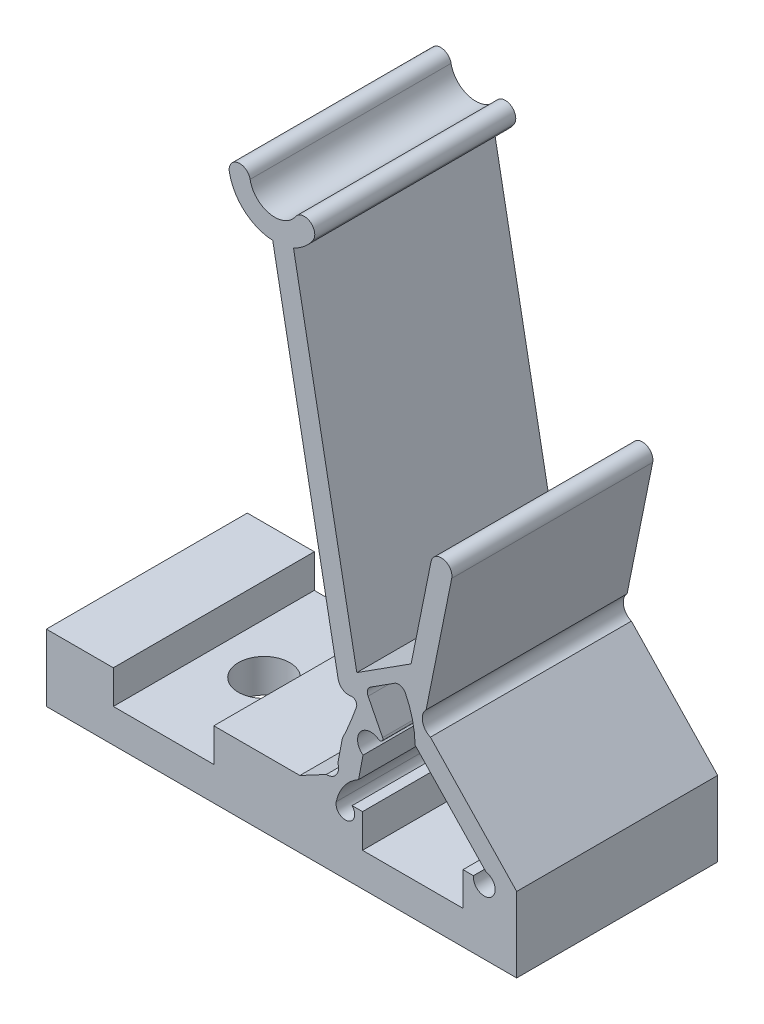
SolidWorks part; units mm, degrees
ref_plane "Front Plane" through (0, 0, 0) normal (0, 0, 1) x (1, 0, 0)
ref_plane "Top Plane" through (0, 0, 0) normal (0, 1, 0) x (1, 0, 0)
ref_plane "Right Plane" through (0, 0, 0) normal (1, 0, 0) x (0, 0, -1)
sketch "Sketch-SkeletonConfigUp" plane through (0, 0, 0) normal (0, 0, 1) x (1, 0, 0)
  line L0 (0, 0) -> (0, -50000) construction
  line L1 (0, 0) -> (7.455, 0.2734) construction
  line L2 (9.9233, 0.3639) -> (10.6101, 4.558) construction
  line L3 (10.6101, 4.558) -> (7.9471, 2.8569) construction
  line L4 (7.9471, 2.8569) -> (7.455, 0.2734) construction
  line L5 (10.6101, 4.558) -> (12.0093, 11.478) construction
  line L6 (7.9471, 2.8569) -> (4.1146, 23.199) construction
  line L7 (7.455, 0.2734) -> (9.9233, 0.3639) construction
  line L8 (-989.4051, -36.2798) -> (9.9233, 0.3639) construction
  point P12 (0, 0)
  point P16 (0, 0)
  point P17 (0, 0)
  dimension "D2" = 7.46
  dimension "D3" = 2.47
  dimension "D4" = 4.25
  dimension "D5" = 78.6
  dimension "D6" = 3.16
  dimension "D7" = 7.06
  dimension "D8" = 20.7
  dimension "D9" = 2.63
  dimension "D10" = 46
  dimension "D11" = 111.9
  dimension "D12" = 92.1
sketch "Sketch-SkeletonConfigDown" plane through (0, 0, 0) normal (0, 0, 1) x (1, 0, 0)
  line L0 (0, 0) -> (0, -50000) construction
  line L1 (0, 0) -> (7.455, 0.2734) construction
  line L2 (9.9233, 0.3639) -> (10.6101, 4.558) construction
  line L3 (10.6101, 4.558) -> (9.7761, 1.5101) construction
  line L4 (9.7761, 1.5101) -> (7.455, 0.2734) construction
  line L5 (10.6101, 4.558) -> (7.0062, 10.6288) construction
  line L6 (9.7761, 1.5101) -> (-6.7111, 14.0265) construction
  line L7 (7.455, 0.2734) -> (9.9233, 0.3639) construction
  line L8 (-993.745, -36.439) -> (9.9233, 0.3639) construction
  point P2 (10.901, 5.6207)
  dimension "D2" = 7.46
  dimension "D3" = 2.47
  dimension "D4" = 4.25
  dimension "D5" = 78.6
  dimension "D6" = 3.16
  dimension "D7" = 7.06
  dimension "D8" = 20.7
  dimension "D9" = 2.63
  dimension "D10" = 46
  dimension "D11" = 111.9
  dimension "D1" = 92.1
sketch "Sketch-ConfigDown" plane through (0, 0, 0) normal (0, 0, 1) x (1, 0, 0)
  line L3 (7.2122, -0.2359) -> (5.3047, -0.3058) construction
  line L4 (9.7761, 1.5101) -> (-6.7111, 14.0265) construction
  line L6 (-200859.4238, -7365.1807) -> (9.9233, 0.3639) construction
  line L7 (7.2122, -0.2359) -> (15.5786, 0.0709) construction
  line L9 (7.455, 0.2734) -> (9.9233, 0.3639) construction
  line L10 (10.9008, 0.9001) -> (10.9374, -0.0993) construction
  line L15 (9.3493, 0.7161) -> (8.352, 0.1848)
  line L18 (8.512, 1.4031) -> (8.9823, 0.5206) construction
  line L19 (6.5762, 10.3736) -> (9.0074, 6.2784)
  line L20 (-5.3148, 12.3387) -> (8.4132, 1.917)
  line L21 (8.2015, 3.3332) -> (-4.7101, 13.1352)
  line L22 (9.7761, 1.5101) -> (7.455, 0.2734) construction
  line L23 (2.9291, 6.0802) -> (3.5338, 6.8767) construction
  line L26 (10.6101, 4.558) -> (14.4503, 0.5299) construction
  line L27 (10.2553, 5.1557) -> (9.3507, 1.85) construction
  line L28 (11.0112, 4.862) -> (15.5786, 0.0709) construction
  line L29 (14.5562, -0.3058) -> (10.7658, 3.6702) construction
  line L30 (12.9938, 1.3331) -> (13.7176, 2.0231) construction
  line L34 (5.3047, -0.3058) -> (5.3047, -3.4808) construction
  line L36 (5.3047, -3.4808) -> (15.5786, -3.4808)
  line L37 (15.5786, -3.4808) -> (15.5786, 0.0709)
  line L38 (-8.0357, 12.2817) -> (-6.0162, 14.9419) construction
  line L39 (10.6101, 4.558) -> (9.7761, 1.5101) construction
  line L40 (9.7556, 3.3297) -> (10.7202, 3.0657) construction
  line L42 (7.4361, 10.8841) -> (10.4021, 5.8879)
  line L43 (8.1032, 7.8014) -> (8.9631, 8.3119) construction
  line L44 (10.6101, 4.558) -> (7.0062, 10.6288) construction
  line L45 (7.7789, -0.3058) -> (5.3047, -0.3058) construction
  line L46 (14.5562, -0.3058) -> (15.5786, -0.3058) construction
  line L47 (13.528, -0.3058) -> (7.7789, -0.3058)
  line L48 (9.0074, 6.2784) -> (8.2015, 3.3332)
  line L49 (15.5786, 0.0709) -> (15.28, 0.3842)
  line L50 (10.7658, 3.6702) -> (9.7307, 4.7558) construction
  line L51 (15.28, 0.3842) -> (14.5562, -0.3058) construction
  line L52 (14.5815, 0.7545) -> (14.7625, 0.927) construction
  line L53 (13.5212, 0.7799) -> (14.2449, 1.4699) construction
  line L54 (11.0112, 4.862) -> (10.4545, 5.4459) construction
  line L55 (10.7911, 4.7305) -> (10.972, 4.903) construction
  line L56 (9.7307, 4.7558) -> (10.4545, 5.4459) construction
  line L57 (10.7658, 3.6702) -> (11.4896, 4.3602) construction
  line L58 (10.7911, 4.7305) -> (10.4292, 4.3855) construction
  line L59 (11.4896, 4.3602) -> (14.2449, 1.4699)
  line L60 (13.5212, 0.7799) -> (10.7658, 3.6702)
  line L61 (10.4545, 5.4459) -> (10.4021, 5.8879)
  line L62 (7.3374, 0.494) -> (7.2199, 0.7146) construction
  line L63 (7.0282, -0.5206) -> (6.3041, -0.9064) construction
  line L64 (7.8818, 1.0673) -> (8.352, 0.1848) construction
  line L65 (6.558, 0.362) -> (7.0282, -0.5206) construction
  line L66 (6.558, 0.362) -> (5.3047, -0.3058)
  line L67 (6.558, 0.362) -> (7.8818, 1.0673) construction
  line L68 (7.3374, 0.494) -> (7.5725, 0.0527) construction
  line L69 (10.2029, 2.304) -> (10.8079, 2.6264) construction
  line L70 (10.6731, 1.4215) -> (11.1125, 1.6556) construction
  line L71 (9.6585, 1.7307) -> (9.541, 1.9513) construction
  line L72 (8.8791, 1.5987) -> (9.3493, 0.7161) construction
  line L73 (10.2029, 2.304) -> (10.6731, 1.4215) construction
  line L74 (9.6585, 1.7307) -> (9.8936, 1.2894) construction
  line L75 (7.8818, 1.0673) -> (8.8791, 1.5987)
  line L76 (8.4132, 1.917) -> (9.4143, 2.4504)
  line L77 (9.6228, 4.1445) -> (11.1323, 2.561)
  line L78 (11.1323, 2.561) -> (11.3028, 2.3822)
  line L79 (-6.7111, 14.0265) -> (-5.0362, 14.2558) construction
  line L80 (-6.7111, 14.0265) -> (-6.7111, -3.4808) construction
  line L81 (5.3047, -3.4808) -> (-6.7111, -3.4808)
  line L82 (-6.7111, -3.4808) -> (-6.7111, -0.3058)
  line L83 (-6.7111, -0.3058) -> (5.3047, -0.3058)
  line L84 (8.8791, 1.5987) -> (10.2029, 2.304) construction
  arc A2 (-7.4311, 13.0782) -> (-5.5316, 14.188) centre (-6.7111, 14.0265) ccw
  arc A3 (-4.7101, 13.1352) -> (-4.5408, 14.3236) centre (-6.7111, 14.0265) ccw
  arc A4 (-8.0357, 12.2817) -> (-7.4311, 13.0782) centre (-7.7334, 12.68) cw
  arc A5 (-4.5408, 14.3236) -> (-5.5316, 14.188) centre (-5.0362, 14.2558) ccw
  arc A6 (-8.0357, 12.2817) -> (-5.3148, 12.3387) centre (-6.7111, 14.0265) ccw
  arc A7 (6.5762, 10.3736) -> (7.4361, 10.8841) centre (7.0062, 10.6288) cw
  arc A8 (15.28, 0.3842) -> (14.2449, 1.4699) centre (15.4863, 1.6171) cw
  arc A9 (14.5562, -0.3058) -> (13.5212, 0.7799) centre (13.3149, -0.453) ccw
  arc A10 (10.4545, 5.4459) -> (11.4896, 4.3602) centre (11.6958, 5.593) ccw
  arc A11 (9.7307, 4.7558) -> (10.7658, 3.6702) centre (9.5245, 3.523) cw
  arc A12 (7.8818, 1.0673) -> (6.558, 0.362) centre (6.7496, 1.5972) cw
  arc A13 (7.0282, -0.5206) -> (8.352, 0.1848) centre (8.1603, -1.0505) cw
  arc A14 (7.0282, -0.5206) -> (7.7789, -0.3058) centre (7.4971, -0.74) ccw
  arc A15 (8.8791, 1.5987) -> (10.2029, 2.304) centre (9.0707, 2.8339) ccw
  arc A16 (9.3493, 0.7161) -> (10.6731, 1.4215) centre (10.4814, 0.1863) cw
  arc A19 (10.2029, 2.304) -> (9.4143, 2.4504) centre (9.8276, 2.4796) ccw
  arc A20 (14.5562, -0.3058) -> (13.528, -0.3058) centre (14.0421, -0.3668) cw
  arc A21 (9.7307, 4.7558) -> (9.6228, 4.1445) centre (9.6795, 4.4497) ccw
  arc A22 (10.6731, 1.4215) -> (11.3028, 2.3822) centre (10.7698, 2.0448) ccw
  point P5 (0, 0)
  point P24 (8.7471, 0.9618)
  point P28 (10.9191, 0.4004)
  point P30 (8.5332, 8.0566)
  point P43 (10.2379, 3.1977)
  point P47 (14.5815, 0.7545)
  point P51 (3.2315, 6.4785)
  point P61 (13.3557, 1.6781)
  dimension "D3" = 2.3812
  dimension "D4" = 4.3812
  dimension "D1" = 1
  dimension "D8" = 1.5
  dimension "D12" = 1.5
  dimension "D5" = 1
  dimension "D6" = 7
  dimension "D2" = 3.175
  dimension "D7" = 1.5
  dimension "D9" = 1.5
  dimension "D10" = 0.25
  dimension "D11" = 1.5
  dimension "D13" = 0.5
  dimension "D14" = 0.5
  dimension "D15" = 45
sketch "Sketch-ConfigUp" plane through (0, 0, 0) normal (0, 0, 1) x (1, 0, 0)
  line L1 (7.3156, 2.2137) -> (7.1042, 1.1037)
  line L2 (8.0635, 0.796) -> (13.3219, 0.9888) construction
  line L3 (10.1988, -0.1264) -> (6.8464, -0.2493) construction
  line L4 (7.9471, 2.8569) -> (7.455, 0.2734) construction
  line L5 (11.5192, 11.5771) -> (10.5754, 6.909)
  line L6 (7.455, 0.2734) -> (9.9233, 0.3639) construction
  line L7 (10.1988, -0.1264) -> (15.5786, 0.0709) construction
  line L9 (10.6101, 4.558) -> (7.9471, 2.8569) construction
  line L10 (8.9451, 0.8283) -> (8.9817, -0.171) construction
  line L11 (7.2099, 1.6587) -> (8.1922, 1.4716) construction
  line L12 (8.7452, 3.96) -> (9.2835, 3.1173) construction
  line L15 (9.9233, 0.3639) -> (10.6101, 4.558) construction
  line L16 (9.7754, 2.5547) -> (10.7623, 2.3931) construction
  line L17 (12.4994, 11.3789) -> (11.2863, 5.379)
  line L18 (10.6101, 4.558) -> (12.0093, 11.478) construction
  line L19 (10.5058, 6.5648) -> (11.486, 6.3666) construction
  line L20 (4.0182, 21.0106) -> (7.1163, 4.5661)
  line L21 (8.0021, 5.2653) -> (5.0009, 21.1957)
  line L22 (7.9471, 2.8569) -> (4.1146, 23.199) construction
  line L23 (6.0985, 9.9681) -> (7.0813, 10.1533) construction
  line L24 (8.3015, 3.6766) -> (10.1621, 4.8651) construction
  line L26 (10.6101, 4.558) -> (14.4503, 0.5299) construction
  line L27 (-200855.0838, -7365.0216) -> (9.9233, 0.3639) construction
  line L30 (10.7658, 3.6702) -> (11.4896, 4.3602) construction
  line L34 (6.8464, -0.2493) -> (6.8464, -3.4808) construction
  line L38 (1.9619, 22.7935) -> (4.1146, 23.199) construction
  line L39 (4.1146, 23.199) -> (5.9236, 21.9636) construction
  line L40 (13.528, -0.3058) -> (7.7789, -0.3058) construction
  line L41 (13.528, -0.3058) -> (7.7789, -0.3058)
  line L42 (11.2489, 5.194) -> (10.7354, 2.6543) construction
  line L43 (10.1621, 4.8651) -> (9.715, 2.6538) construction
  line L44 (6.8464, -0.2493) -> (5.1916, -0.31) construction
  line L45 (8.0635, 0.796) -> (8.0865, 0.9166) construction
  line L46 (8.0635, 0.796) -> (7.8058, -0.5569) construction
  line L47 (7.2094, 0.3201) -> (6.9638, 0.3669) construction
  line L48 (7.2094, 0.3201) -> (7.7006, 0.2266) construction
  line L49 (6.8235, -0.3698) -> (7.8058, -0.5569) construction
  line L50 (7.4382, 2.8574) -> (7.5963, 3.6872) construction
  line L51 (8.3979, 2.5516) -> (8.5786, 3.5001) construction
  line L52 (7.3156, 2.2137) -> (8.2979, 2.0266) construction
  line L53 (7.5963, 3.6872) -> (8.5786, 3.5001) construction
  line L54 (7.7015, 2.9037) -> (8.1927, 2.8101) construction
  line L55 (7.7015, 2.9037) -> (7.4559, 2.9505) construction
  line L56 (8.1564, 2.8991) -> (7.6708, 3.0185) construction
  line L57 (7.1163, 4.5661) -> (7.4382, 2.8574) construction
  line L58 (11.2863, 5.379) -> (10.3061, 5.5772) construction
  line L59 (7.4382, 2.8574) -> (7.3156, 2.2137) construction
  line L60 (7.8068, 2.1202) -> (8.6839, 3.337) construction
  line L61 (8.2979, 2.0266) -> (8.0865, 0.9166)
  line L62 (7.1042, 1.1037) -> (8.0865, 0.9166) construction
  line L69 (10.8552, 4.5085) -> (11.1002, 4.4589) construction
  line L70 (7.7789, -0.3058) -> (5.3047, -0.3058) construction
  line L71 (7.7789, -0.3058) -> (5.3047, -0.3058) construction
  line L73 (7.1042, 1.1037) -> (6.8464, -0.2493) construction
  line L74 (10.2687, 5.3922) -> (11.2489, 5.194) construction
  line L75 (9.9714, 3.922) -> (10.9516, 3.7238) construction
  line L76 (10.8552, 4.5085) -> (10.3651, 4.6076) construction
  line L77 (8.3979, 2.5516) -> (8.2979, 2.0266) construction
  line L78 (9.5833, 3.3088) -> (8.3979, 2.5516) construction
  line L79 (8.0021, 5.2653) -> (10.5754, 6.909)
  line L80 (8.0021, 5.2653) -> (8.3015, 3.6766) construction
  line L81 (10.5058, 6.5648) -> (10.1621, 4.8651) construction
  line L82 (10.5058, 6.5648) -> (10.5754, 6.909) construction
  line L83 (11.4896, 4.3602) -> (10.7658, 3.6702) construction
  line L84 (11.1158, 4.8153) -> (10.6255, 4.7174) construction
  line L106 (6.558, 0.362) -> (5.3047, -0.3058)
  line L107 (5.3047, -0.3058) -> (-6.7111, -0.3058)
  line L108 (-6.7111, -0.3058) -> (-6.7111, -3.4808)
  line L109 (-6.7111, -3.4808) -> (15.5786, -3.4808)
  line L110 (15.5786, -3.4808) -> (15.5786, 0.0709)
  line L112 (15.5786, 0.0709) -> (11.4896, 4.3602)
  line L114 (11.1277, 4.0152) -> (10.7962, 5.4781) construction
  line L115 (9.5833, 3.3088) -> (10.5323, 3.915) construction
  line L116 (13.3219, 0.9888) -> (10.7658, 3.6702)
  line L117 (10.7658, 3.6702) -> (10.5323, 3.915) construction
  line L118 (10.6101, 4.558) -> (7.9471, 2.8569) construction
  line L119 (8.6839, 3.337) -> (9.4161, 2.8092) construction
  line L120 (8.6839, 3.337) -> (7.8068, 3.9692) construction
  line L121 (9.0288, 3.0406) -> (8.2979, 2.0266) construction
  line L123 (9.7888, 5.7212) -> (8.6571, 4.9983)
  line L124 (8.5388, 4.5661) -> (9.2253, 3.2085)
  line L126 (13.3219, 0.9888) -> (14.1275, 0.1438)
  line L127 (11.2489, 5.194) -> (11.2863, 5.379) construction
  arc A0 (11.5192, 11.5771) -> (12.4994, 11.3789) centre (12.0093, 11.478) cw
  arc A2 (2.9446, 22.9786) -> (5.0978, 22.5276) centre (4.1146, 23.199) ccw
  arc A3 (5.0009, 21.1957) -> (5.9236, 21.9636) centre (4.1146, 23.199) ccw
  arc A4 (1.9619, 22.7935) -> (2.9446, 22.9786) centre (2.4533, 22.886) cw
  arc A5 (5.9236, 21.9636) -> (5.0978, 22.5276) centre (5.5107, 22.2456) ccw
  arc A6 (1.9619, 22.7935) -> (4.0182, 21.0106) centre (4.1146, 23.199) ccw
  arc A7 (13.528, -0.3058) -> (14.5562, -0.3058) centre (14.0421, -0.3668) ccw construction
  arc A8 (13.528, -0.3058) -> (14.1275, 0.1438) centre (14.0421, -0.3668) ccw
  arc A9 (7.1042, 1.1037) -> (6.8235, -0.3698) centre (5.9815, 0.554) cw construction
  arc A10 (7.8058, -0.5569) -> (8.0865, 0.9166) centre (8.9285, -0.0073) cw construction
  arc A11 (7.3156, 2.2137) -> (7.5963, 3.6872) centre (6.4736, 3.1376) ccw construction
  arc A12 (8.2979, 2.0266) -> (8.5786, 3.5001) centre (9.4206, 2.5762) cw construction
  arc A13 (11.2489, 5.194) -> (10.9516, 3.7238) centre (12.0804, 4.2607) ccw construction
  arc A14 (10.2687, 5.3922) -> (9.9714, 3.922) centre (9.1399, 4.8553) cw construction
  arc A15 (8.0865, 0.9166) -> (7.0282, -0.5206) centre (9.1391, -0.9668) ccw
  arc A16 (7.1042, 1.1037) -> (6.558, 0.362) centre (6.5823, 0.916) cw
  arc A17 (7.0282, -0.5206) -> (7.7789, -0.3058) centre (7.4604, -0.612) ccw
  arc A18 (11.4896, 4.3602) -> (11.2863, 5.379) centre (11.7287, 4.9376) cw
  arc A19 (8.2979, 2.0266) -> (9.0288, 3.0406) centre (8.6634, 2.5336) cw
  arc A21 (7.3156, 2.2137) -> (7.9864, 3.8397) centre (-8.9784, 9.887) ccw
  arc A22 (7.9864, 3.8397) -> (7.7104, 4.1617) centre (7.7563, 3.9218) ccw
  arc A23 (10.7658, 3.6702) -> (10.3061, 5.5772) centre (6.3229, 3.6081) ccw
  arc A24 (7.7104, 4.1617) -> (7.1163, 4.5661) centre (7.615, 4.66) cw
  arc A25 (9.0288, 3.0406) -> (9.2253, 3.2085) centre (9.1066, 3.1485) ccw
  arc A27 (10.3061, 5.5772) -> (9.7888, 5.7212) centre (9.9829, 5.4174) ccw
  arc A39 (8.6571, 4.9983) -> (8.5388, 4.5661) centre (8.8369, 4.7168) ccw
  point P6 (0, 0)
  point P25 (9.0144, 3.5387)
  point P27 (7.701, 1.5651)
  point P28 (8.9634, 0.3287)
  point P36 (10.2689, 2.4739)
  point P38 (10.9959, 6.4657)
  point P51 (6.5899, 10.0607)
  point P59 (0, 0)
  point P61 (11.1277, 4.0152)
  point P65 (5.776, 23.512)
  point P71 (5.776, 23.512)
  point P82 (0, 0)
  point P86 (0, 0)
  point P107 (0, 0)
  point P120 (5.7693, 23.1882)
  point P122 (0, 0)
  point P123 (5.3047, 23.4195)
  point P126 (0, 0)
  point P127 (0, 0)
  point P128 (0, 0)
  point P163 (5.0978, 22.5276)
  dimension "D3" = 2.3812
  dimension "D4" = 4.3812
  dimension "D13" = 0.625
  dimension "D17" = 0.625
  dimension "D1" = 1
  dimension "D5" = 7
  dimension "D10" = 1.5
  dimension "D11" = 0.25
  dimension "D8" = 1.5
  dimension "D9" = 0.25
  dimension "D6" = 1.5
  dimension "D7" = 0.25
  dimension "D12" = 1.5
  dimension "D15" = 0.5
  dimension "D16" = 1.5
  dimension "D18" = 0.5
  dimension "D19" = 25
  dimension "D20" = 1.5
  dimension "D14" = 45
extrude "Boss-ConfigUp" add sketch "Sketch-ConfigUp" along normal blind 9.525
sketch "Sketch2" plane through (0.0043, -0.3058, 0) normal (0, -1, 0) x (-1, 0, 0)
  line L1 (-13.0304, 0) -> (-8.2679, 0)
  line L2 (-13.0304, 0) -> (-13.0304, -9.525)
  line L3 (-13.0304, -9.525) -> (-8.2679, -9.525)
  line L4 (-8.2679, 0) -> (-8.2679, -9.525)
  line L5 (-13.5237, 0) -> (-13.0304, 0) construction
  line L7 (-8.2679, 0) -> (-7.7746, 0) construction
  line L10 (-15.5743, -4.7625) -> (6.7155, -4.7625) construction
  line L12 (-13.0304, 0) -> (-8.2679, -9.525) construction
  line L17 (-13.0304, -9.525) -> (-8.2679, 0) construction
  line L18 (6.7155, 0) -> (-15.5743, 0) construction
  line L19 (6.7155, -9.525) -> (6.7155, 0) construction
  line L20 (3.5405, -9.525) -> (3.5405, 0)
  line L21 (3.5405, -9.525) -> (-1.222, -9.525)
  line L22 (3.5405, 0) -> (-1.222, 0)
  line L23 (-1.222, -9.525) -> (-1.222, 0)
  line L24 (3.5405, -9.525) -> (-1.222, 0) construction
  line L25 (3.5405, 0) -> (-1.222, -9.525) construction
  line L26 (6.7155, -9.525) -> (-15.5743, -9.525) construction
  line L27 (-15.5743, -9.525) -> (-15.5743, 0) construction
  point P4 (-10.6492, -4.7625)
  point P26 (1.1592, -4.7625)
  dimension "D1" = 4.7625
  dimension "D2" = 3.175
extrude "Cut-NutSlot" cut sketch "Sketch2" along normal blind 1.5875
hole_wizard "#2 Clearance Hole1" positions "Sketch4" profile "Sketch3" hole size "#2" standard "ANSI Inch" end condition up to next
sketch "Sketch4" plane through (0, -3.4808, 0) normal (0, -1, 0) x (-1, 0, 0)
  line L16 (-13.0347, 0) -> (-8.2722, -9.525) construction
  point P40 (-10.6535, -4.7625)
  point P44 (1.1549, -4.7625)
  point P47 (-10.6535, -4.7625)
  point P48 (1.1549, -4.7625)
sketch "Sketch3" plane through (10.6535, -3.4808, 4.7625) normal (1, 0, 0) x (0, 0, -1)
  line L0 (0, 0) -> (0, 1.5875)
  line L1 (0, 1.5875) -> (1.2192, 1.5875)
  line L2 (1.2192, 1.5875) -> (1.2192, 0)
  line L5 (1.2192, 0) -> (0, 0)
  line L11 (0, -6.35) -> (0, 107.95) construction
  dimension "Thru Hole Dia." = 2.4384
  dimension "Thru Hole Depth" = 1.5875
ref_plane "Plane-Midplane" through (0, 0, 4.7625) normal (0, 0, -1) x (-1, 0, 0)
equation "\"axle-diameter\"=2"
equation "\"switch-thickness\"=12"
equation "\"base-width\"=4.0"
equation "\"axle-bushing-radius\"=3"
equation "\"clearance\"= 0.25"
equation "\"arm-width\"=1.0"
equation "\"min-diameter\"=70"
equation "\"alpha\"=92.1"
equation "\"beta\"=26.0"
equation "\"gamma\"=78.6"
equation "\"delta\"=111.9"
equation "\"epsilon\"=46.0"
equation "\"eta\"=-228.1"
equation "\"l_AB\"=2.47"
equation "\"l_AC\"=2.63"
equation "\"l_BD\"=4.25"
equation "\"l_CD\"=3.16"
equation "\"l_CE\"=20.70"
equation "\"l_DF\"=7.06"
equation "\"l_OA\"=7.46"
equation "\"D2@Sketch-SkeletonConfigUp\" = \"l_OA\""
equation "\"D3@Sketch-SkeletonConfigUp\" = \"l_AB\""
equation "\"D4@Sketch-SkeletonConfigUp\" = \"l_BD\""
equation "\"D5@Sketch-SkeletonConfigUp\" = \"gamma\""
equation "\"D6@Sketch-SkeletonConfigUp\" = \"l_CD\""
equation "\"D7@Sketch-SkeletonConfigUp\" = \"l_DF\""
equation "\"D8@Sketch-SkeletonConfigUp\" = \"l_CE\""
equation "\"D9@Sketch-SkeletonConfigUp\" = \"l_AC\""
equation "\"D_groove\"=2.3812"
equation "\"D3@Sketch-ConfigUp\" = \"D_groove\""
equation "\"D4@Sketch-ConfigUp\" = \"D_groove\" + 2 * \"arm-width\""
equation "\"D7@Sketch-SkeletonConfigDown\" = \"l_DF\""
equation "\"D6@Sketch-SkeletonConfigDown\" = \"l_CD\""
equation "\"D2@Sketch-SkeletonConfigDown\" = \"l_OA\""
equation "\"D3@Sketch-SkeletonConfigDown\" = \"l_AB\""
equation "\"D9@Sketch-SkeletonConfigDown\" = \"l_AC\""
equation "\"D8@Sketch-SkeletonConfigDown\" = \"l_CE\""
equation "\"D5@Sketch-SkeletonConfigDown\" = \"gamma\""
equation "\"D4@Sketch-SkeletonConfigDown\" = \"l_BD\""
equation "\"D1@Sketch-SkeletonConfigDown\" = \"alpha\""
equation "\"D5@Sketch-ConfigDown\" = \"arm-width\""
equation "\"hinge_length\"=1.5"
equation "\"hinge_depth\"=0.25"
equation "\"D9@Sketch-ConfigDown\" = \"hinge_length\""
equation "\"D10@Sketch-ConfigDown\" = \"hinge_depth\""
equation "\"D8@Sketch-ConfigDown\" = \"hinge_length\""
equation "\"D11@Sketch-ConfigDown\" = \"hinge_length\""
equation "\"D12@Sketch-ConfigDown\" = \"hinge_length\""
equation "\"D10@Sketch-ConfigUp\" = \"hinge_length\""
equation "\"D11@Sketch-ConfigUp\" = \"hinge_depth\""
equation "\"D8@Sketch-ConfigUp\" = \"hinge_length\""
equation "\"D9@Sketch-ConfigUp\" = \"hinge_depth\""
equation "\"D6@Sketch-ConfigUp\" = \"hinge_length\""
equation "\"D7@Sketch-ConfigUp\" = \"hinge_depth\""
equation "\"D10@Sketch-SkeletonConfigUp\"=\"epsilon\""
equation "\"D11@Sketch-SkeletonConfigUp\"=\"delta\""
equation "\"D12@Sketch-SkeletonConfigUp\"=\"alpha\""
equation "\"D11@Sketch-SkeletonConfigDown\"=\"delta\""
equation "\"D10@Sketch-SkeletonConfigDown\"=\"epsilon\""
equation "\"D15@Sketch-ConfigUp\"=2*\"hinge_depth\""
equation "\"D16@Sketch-ConfigUp\"=\"hinge_length\""
equation "\"D18@Sketch-ConfigUp\"=2*\"hinge_depth\""
equation "\"D20@Sketch-ConfigUp\"=\"hinge_length\""
